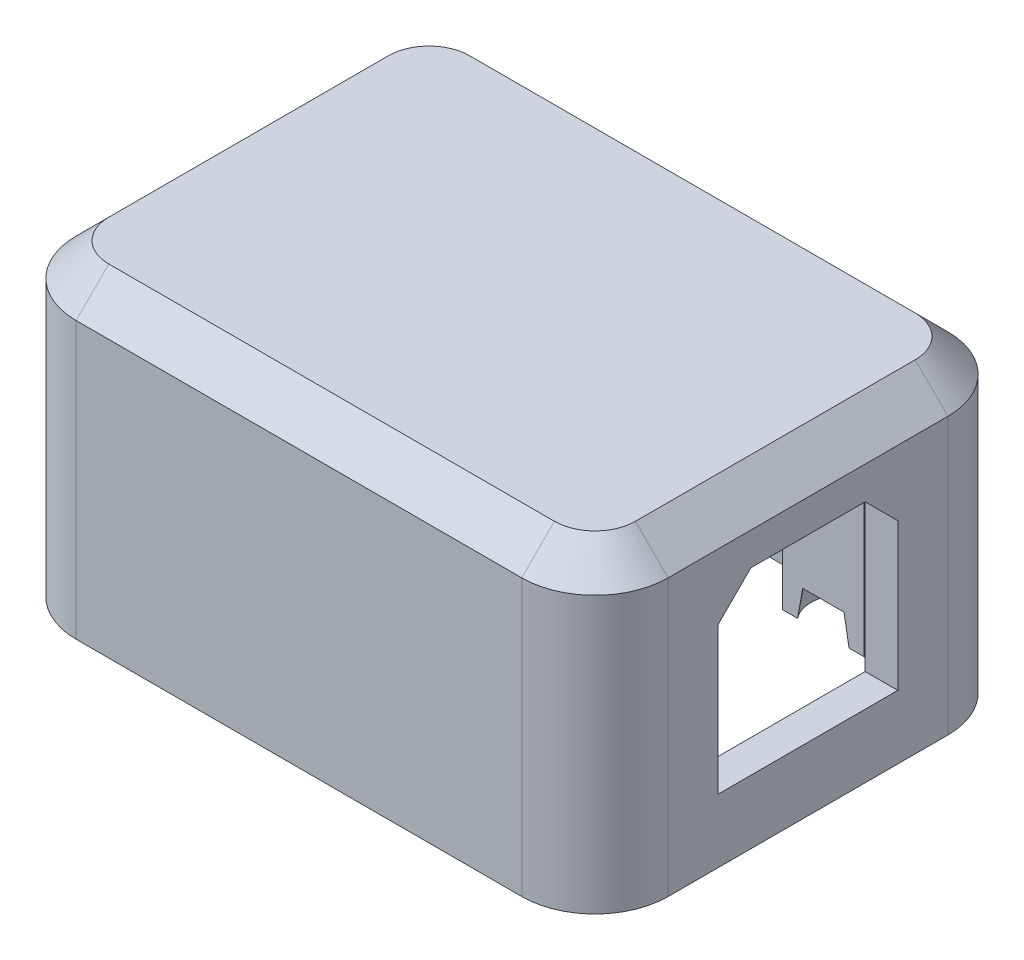
SolidWorks part; units mm, degrees
ref_plane "Front Plane" through (0, 0, 0) normal (0, 0, 1) x (1, 0, 0)
ref_plane "Top Plane" through (0, 0, 0) normal (0, 1, 0) x (1, 0, 0)
ref_plane "Right Plane" through (0, 0, 0) normal (1, 0, 0) x (0, 0, -1)
sketch "pcb-outline" plane through (0, 0, 0) normal (0, 1, 0) x (1, 0, 0)
  line L0 (27.94, 19.05) -> (27.94, 2.54) construction
  line L1 (2.23, 0) -> (29.52, 0)
  line L2 (0, 2.23) -> (0, 19.36)
  line L3 (2.23, 21.59) -> (29.52, 21.59)
  line L4 (31.75, 2.23) -> (31.75, 19.36)
  arc A0 (2.23, 0) -> (0, 2.23) centre (2.23, 2.23) cw
  arc A1 (29.52, 0) -> (31.75, 2.23) centre (29.52, 2.23) ccw
  arc A2 (29.52, 21.59) -> (31.75, 19.36) centre (29.52, 19.36) cw
  arc A3 (0, 19.36) -> (2.23, 21.59) centre (2.23, 19.36) cw
  circle A4 centre (27.94, 19.05) radius 1.795
  circle A5 centre (27.94, 2.54) radius 1.795
  point P7 (0, 0)
  point P10 (31.75, 0)
  point P15 (0, 21.59)
  point P20 (0, 10.795)
  point P21 (27.94, 10.795)
  dimension "D3" = 2.23
  dimension "D6" = 3.59
  dimension "D1" = 21.59
  dimension "D2" = 31.75
  dimension "D4" = 16.51
  dimension "D5" = 27.94
sketch "Sketch2" plane through (0, 0, 0) normal (0, 1, 0) x (1, 0, 0)
  line L0 (-0.25, 19.36) -> (-0.25, 2.23)
  line L1 (2.23, -0.25) -> (29.52, -0.25)
  line L2 (32, 2.23) -> (32, 19.36)
  line L3 (29.52, 21.84) -> (2.23, 21.84)
  line L4 (31.75, 2.23) -> (31.75, 19.36) construction
  arc A0 (-0.25, 2.23) -> (2.23, -0.25) centre (2.23, 2.23) ccw
  arc A1 (29.52, -0.25) -> (32, 2.23) centre (29.52, 2.23) ccw
  arc A2 (32, 19.36) -> (29.52, 21.84) centre (29.52, 19.36) ccw
  arc A3 (2.23, 21.84) -> (-0.25, 19.36) centre (2.23, 19.36) ccw
  dimension "D1" = 0.25
extrude "main-extrusion" add sketch "Sketch2" along normal blind 14 thin
sketch "Sketch3" plane through (0, 14, 0) normal (0, -1, 0) x (1, 0, 0)
  line L0 (-2.25, -19.36) -> (-2.25, -2.23)
  line L1 (2.23, 2.25) -> (29.52, 2.25)
  line L2 (34, -2.23) -> (34, -19.36)
  line L3 (29.52, -23.84) -> (2.23, -23.84)
  arc A0 (-2.25, -2.23) -> (2.23, 2.25) centre (2.23, -2.23) cw
  arc A1 (29.52, 2.25) -> (34, -2.23) centre (29.52, -2.23) cw
  arc A2 (34, -19.36) -> (29.52, -23.84) centre (29.52, -19.36) cw
  arc A3 (2.23, -23.84) -> (-2.25, -19.36) centre (2.23, -19.36) cw
extrude "tapered-bottom" add sketch "Sketch3" against normal blind 2 draft 45
sketch "Sketch4" plane through (0, 14, 0) normal (0, 1, 0) x (1, 0, 0)
  line L7 (0, 2.23) -> (0, 19.36) construction
  line L8 (2.23, -0.25) -> (29.52, -0.25) construction
  line L9 (17, 21.84) -> (9, 21.84)
  line L10 (17, 21.84) -> (17, 18.795)
  line L11 (17, 18.795) -> (9, 18.795)
  line L12 (9, 21.84) -> (9, 18.795)
  line L13 (9, -0.25) -> (17, -0.25)
  line L14 (9, -0.25) -> (9, 2.795)
  line L15 (9, 2.795) -> (17, 2.795)
  line L16 (17, -0.25) -> (17, 2.795)
  line L18 (29.52, 21.84) -> (2.23, 21.84) construction
  circle A0 centre (27.94, 19.05) radius 2.795
  circle A1 centre (27.94, 2.54) radius 2.795
  circle A3 centre (27.94, 19.05) radius 1.795 construction
  dimension "D1" = 1
  dimension "D2" = 16
  dimension "D4" = 9
  dimension "D5" = 17
extrude "PCB-support" add sketch "Sketch4" against normal offset from surface (13.75 mm away) 0.25 up to face at (15.875, 0, -10.795)
sketch "Sketch5" plane through (0, 0, 0) normal (0, 1, 0) x (1, 0, 0)
  circle A0 centre (27.94, 19.05) radius 2.045
  circle A1 centre (27.94, 2.54) radius 2.045
  circle A3 centre (27.94, 19.05) radius 1.795 construction
  dimension "D1" = 0.25
extrude "guide-pin-cutout" cut sketch "Sketch5" along normal blind 2 draft 7.5
sketch "Sketch12" plane through (0, 14, 0) normal (0, -1, 0) x (1, 0, 0)
  line L0 (27.94, -19.05) -> (27.94, -2.54) construction
  line L1 (30.4374, -3.795) -> (25.4426, -3.795)
  line L2 (30.4374, -3.795) -> (30.4374, -17.795)
  line L3 (30.4374, -17.795) -> (25.4426, -17.795)
  line L4 (25.4426, -3.795) -> (25.4426, -17.795)
  arc A0 (27.7729, 0.25) -> (28.1071, 0.25) centre (27.94, -2.54) ccw construction
  arc A1 (28.1071, -21.84) -> (27.7729, -21.84) centre (27.94, -19.05) ccw construction
  point P10 (30.2655, -4.0905)
  point P11 (27.94, -3.795)
  dimension "D1" = 14
extrude "Cut-Extrude6" cut sketch "Sketch12" along normal up to next
sketch "Sketch11" plane through (0, 14, 0) normal (0, -1, 0) x (1, 0, 0)
  line L0 (32, -2.23) -> (32, -19.36) construction
  line L1 (32, -7.295) -> (25, -7.295)
  line L2 (32, -7.295) -> (32, -14.295)
  line L3 (32, -14.295) -> (25, -14.295)
  line L4 (25, -7.295) -> (25, -14.295)
  line L5 (-0.25, -19.36) -> (-0.25, -2.23) construction
  point P8 (-0.25, -10.795)
  point P9 (25, -10.795)
  dimension "D1" = 7
  dimension "D2" = 7
extrude "Boss-Extrude1" add sketch "Sketch11" along normal offset from surface (2 mm away) 12 up to face at (15.875, 0, -10.795)
ref_plane "Plane1" through (29.52, 0, 0) normal (1, 0, 0) x (0, 0, -1)
sketch "hook" plane through (29.52, 0, 0) normal (1, 0, 0) x (0, 0, -1)
  line L2 (22.84, -2.9) -> (22.84, -1.3)
  line L4 (22.84, 0) -> (22.84, -0.2)
  line L5 (22.84, 0) -> (23.84, 0)
  line L6 (23.84, 0) -> (23.84, -2.9)
  line L7 (23.84, -2.9) -> (22.84, -2.9)
  arc A0 (22.84, -0.2) -> (22.84, -1.3) centre (22.5829, -0.75) cw
  point P11 (23.19, -0.75)
  dimension "D1" = 0.75
  dimension "D2" = 2.9
  dimension "D3" = 1.1
  dimension "D4" = 0.35
  dimension "D5" = 1
sketch "path" plane through (0, 0, 0) normal (0, -1, 0) x (1, 0, 0)
  line L0 (2.23, 0.25) -> (29.52, 0.25)
  line L1 (32, -2.23) -> (32, -19.36)
  line L2 (29.52, -21.84) -> (2.23, -21.84)
  line L3 (-0.25, -19.36) -> (-0.25, -2.23)
  arc A0 (29.52, 0.25) -> (32, -2.23) centre (29.52, -2.23) cw
  arc A1 (32, -19.36) -> (29.52, -21.84) centre (29.52, -19.36) cw
  arc A2 (2.23, -21.84) -> (-0.25, -19.36) centre (2.23, -19.36) cw
  arc A3 (-0.25, -2.23) -> (2.23, 0.25) centre (2.23, -2.23) cw
sweep "top-hook" add profiles "hook" path "path"
sketch "Sketch8" plane through (-2.25, 0, 0) normal (-1, 0, 0) x (0, 0, 1)
  line L0 (-19.36, 14) -> (-2.23, 14) construction
  circle A0 centre (-10.795, 7) radius 6.5
  point P5 (-10.795, 14)
  dimension "D1" = 13
  dimension "D2" = 7
sketch "Sketch9" plane through (-2.25, 0, 0) normal (-1, 0, 0) x (0, 0, 1)
  line L0 (-18.295, 7) -> (-18.295, 12)
  line L1 (-16.295, 14) -> (-5.295, 14)
  line L2 (-3.295, 12) -> (-3.295, 7)
  arc A0 (-3.295, 7) -> (-18.295, 7) centre (-10.795, 7) cw
  arc A1 (-18.295, 12) -> (-16.295, 14) centre (-16.295, 12) cw
  arc A2 (-5.295, 14) -> (-3.295, 12) centre (-5.295, 12) cw
  circle A3 centre (-10.795, 7) radius 6.5 construction
  dimension "D1" = 1
  dimension "D2" = 7
  dimension "D3" = 2
extrude "Cut-Extrude2" cut sketch "Sketch8" against normal up to next
extrude "Cut-Extrude4" cut sketch "Sketch9" against normal blind 0.5
sketch "Sketch10" plane through (34, 0, 0) normal (1, 0, 0) x (0, 0, -1)
  line L0 (5.295, 1) -> (16.295, 1)
  line L1 (16.295, 1) -> (16.295, 10)
  line L2 (16.295, 10) -> (14.295, 12)
  line L3 (14.295, 12) -> (7.295, 12)
  line L4 (7.295, 12) -> (5.295, 10)
  line L5 (5.295, 10) -> (5.295, 1)
  line L6 (2.23, 14) -> (19.36, 14) construction
  line L7 (2.23, 0) -> (19.36, 0) construction
  point P9 (10.795, 14)
  point P10 (10.795, 12)
  dimension "D1" = 11
  dimension "D2" = 11
  dimension "D3" = 2
  dimension "D4" = 1
extrude "Cut-Extrude5" cut sketch "Sketch10" against normal up to next
chamfer "Chamfer1" distance 0.5 angle 45 8 edges at (15.875, -2.9, -22.84) (-0.2307, -2.9, -21.8207) (31.9807, -2.9, -21.8207) (-1.25, -2.9, -10.795) (33, -2.9, -10.795) (-0.2307, -2.9, 0.2307) (31.9807, -2.9, 0.2307) (15.875, -2.9, 1.25)
